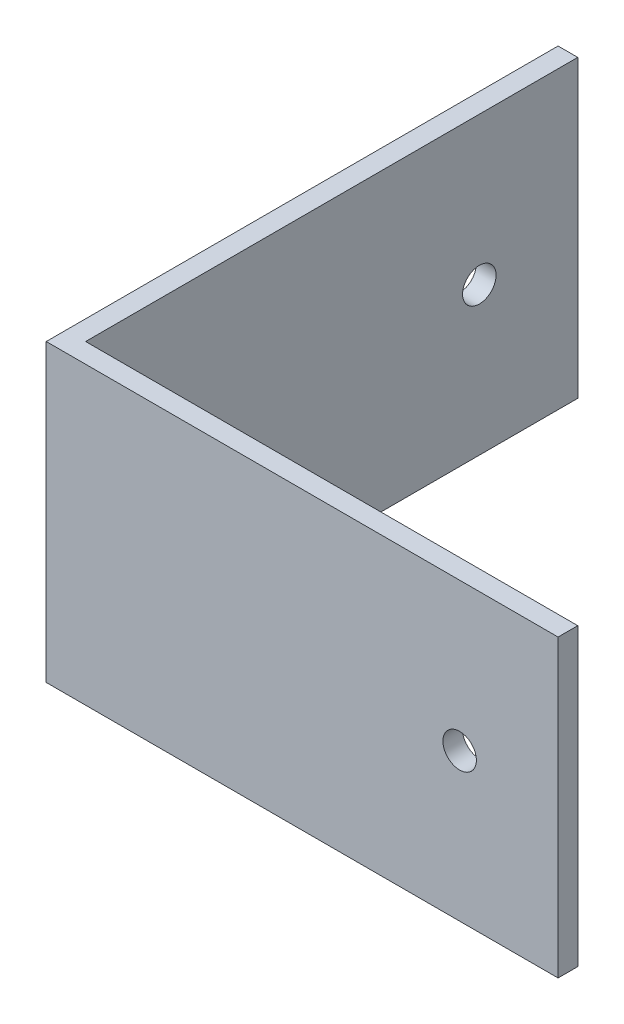
SolidWorks part; units mm, degrees
ref_plane "Front Plane" through (0, 0, 0) normal (0, 0, 1) x (1, 0, 0)
ref_plane "Top Plane" through (0, 0, 0) normal (0, 1, 0) x (1, 0, 0)
ref_plane "Right Plane" through (0, 0, 0) normal (1, 0, 0) x (0, 0, -1)
sketch "Sketch1" plane through (0, 0, 0) normal (0, 0, 1) x (1, 0, 0)
  line L1 (-12.5, 7.5) -> (12.5, 7.5)
  line L2 (-12.5, 7.5) -> (-12.5, -7.5)
  line L3 (-12.5, -7.5) -> (12.5, -7.5)
  line L4 (12.5, 7.5) -> (12.5, -7.5)
  line L5 (-12.5, 7.5) -> (12.5, -7.5) construction
  line L6 (-12.5, -7.5) -> (12.5, 7.5) construction
  circle A1 centre (7.5, 0) radius 0.85
  point P0 (0, 0)
  point P8 (0, 0)
  dimension "D3" = 1.7
  dimension "D1" = 15
  dimension "D2" = 25
  dimension "D4" = 5
extrude "Boss-Extrude1" add sketch "Sketch1" along normal blind 1
sketch "Sketch2" plane through (-12.5, 0, 0) normal (-1, 0, 0) x (0, 0, 1)
  line L1 (1, 7.5) -> (-25, 7.5)
  line L2 (1, 7.5) -> (1, -7.5)
  line L3 (1, -7.5) -> (-25, -7.5)
  line L4 (-25, 7.5) -> (-25, -7.5)
  circle A0 centre (-20, 0) radius 0.85
  point P7 (0, 0)
  point P9 (-21.727, -1.3846)
  dimension "D3" = 1.7
  dimension "D1" = 26
  dimension "D2" = 15
  dimension "D4" = 5
  dimension "D5" = 7.5
extrude "Boss-Extrude2" add sketch "Sketch2" along normal blind 1
